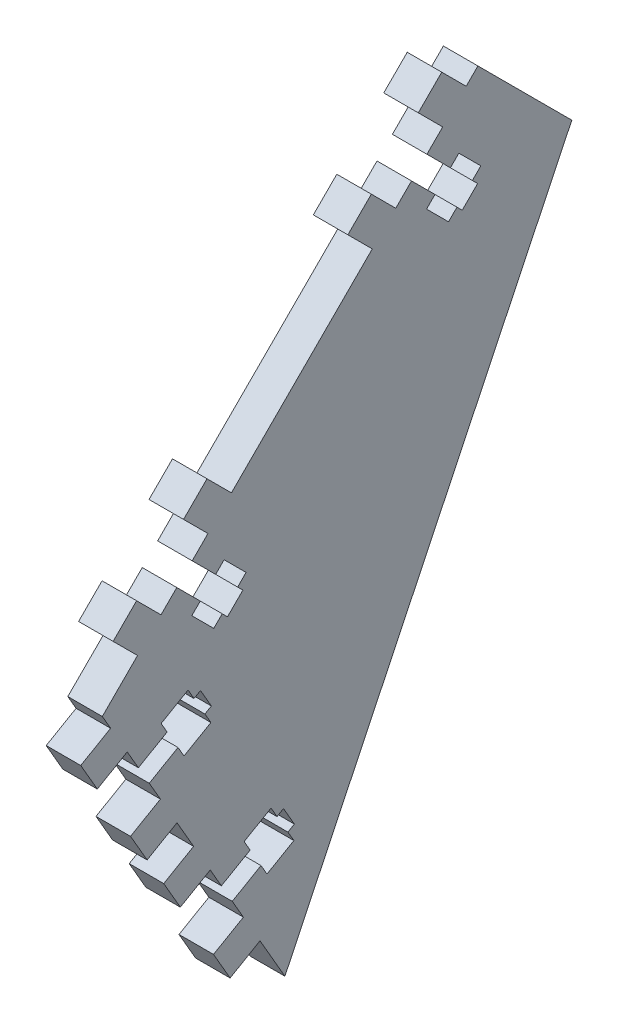
SolidWorks part; units mm, degrees
material "Acrylic (Blue)"
ref_plane "Front Plane" through (0, 0, 0) normal (0, 0, 1) x (1, 0, 0)
ref_plane "Top Plane" through (0, 0, 0) normal (0, 1, 0) x (1, 0, 0)
ref_plane "Right Plane" through (0, 0, 0) normal (1, 0, 0) x (0, 0, -1)
sketch "Sketch1" plane through (0, 0, 0) normal (1, 0, 0) x (0, 0, -1)
  line L0 (0, 0) -> (-34.925, 60.4919)
  line L2 (0, 0) -> (0, 247.8388) construction
  line L3 (0, 0) -> (101.6, 0) construction
  line L4 (0, 0) -> (54.8776, 114.3734)
  line L9 (54.8776, 114.3734) -> (36.917, 132.3339)
  line L10 (36.917, 132.3339) -> (-34.925, 60.4919)
  line B0 (24.219, 119.6358) -> (28.7091, 115.1457) construction
  line B1 (28.7091, 115.1457) -> (27.0926, 113.5293) construction
  line B2 (27.0926, 113.5293) -> (31.2954, 109.3265) construction
  line B3 (31.2954, 109.3265) -> (32.9119, 110.943) construction
  line B4 (32.9119, 110.943) -> (33.9176, 109.9372) construction
  line B5 (33.9176, 109.9372) -> (36.8632, 112.8827) construction
  line B6 (36.8632, 112.8827) -> (35.8574, 113.8885) construction
  line B7 (35.8574, 113.8885) -> (37.4738, 115.5049) construction
  line B8 (37.4738, 115.5049) -> (33.2711, 119.7077) construction
  line B9 (33.2711, 119.7077) -> (31.6546, 118.0912) construction
  line B10 (31.6546, 118.0912) -> (27.1645, 122.5814) construction
  line B11 (30.1819, 125.5987) -> (25.5121, 130.2685) construction
  line B12 (25.5121, 130.2685) -> (30.0023, 134.7586) construction
  line B13 (30.0023, 134.7586) -> (34.672, 130.0889) construction
  line B14 (24.219, 119.6358) -> (21.2016, 116.6185) construction
  line B15 (21.2016, 116.6185) -> (16.5319, 121.2882) construction
  line B16 (16.5319, 121.2882) -> (12.0417, 116.7981) construction
  line B17 (12.0417, 116.7981) -> (16.7115, 112.1283) construction
  line B18 (27.1645, 122.5814) -> (24.219, 119.6358) construction
  line B19 (-20.6823, 74.7346) -> (-16.1922, 70.2444) construction
  line B20 (-16.1922, 70.2444) -> (-17.8086, 68.628) construction
  line B21 (-17.8086, 68.628) -> (-13.6059, 64.4252) construction
  line B22 (-13.6059, 64.4252) -> (-11.9894, 66.0417) construction
  line B23 (-11.9894, 66.0417) -> (-10.9836, 65.0359) construction
  line B24 (-10.9836, 65.0359) -> (-8.0381, 67.9814) construction
  line B25 (-8.0381, 67.9814) -> (-9.0439, 68.9872) construction
  line B26 (-9.0439, 68.9872) -> (-7.4275, 70.6036) construction
  line B27 (-7.4275, 70.6036) -> (-11.6302, 74.8064) construction
  line B28 (-11.6302, 74.8064) -> (-13.2467, 73.19) construction
  line B29 (-13.2467, 73.19) -> (-17.7368, 77.6801) construction
  line B30 (-14.7194, 80.6975) -> (-19.3892, 85.3672) construction
  line B31 (-19.3892, 85.3672) -> (-14.899, 89.8573) construction
  line B32 (-14.899, 89.8573) -> (-10.2293, 85.1876) construction
  line B33 (-23.6997, 71.7172) -> (-28.3694, 76.3869) construction
  line B34 (-28.3694, 76.3869) -> (-32.8595, 71.8968) construction
  line B35 (-32.8595, 71.8968) -> (-28.1898, 67.2271) construction
  line B36 (-17.7368, 77.6801) -> (-20.6823, 74.7346) construction
  line B37 (-25.9461, 44.94) -> (-20.4468, 48.115) construction
  line B38 (-20.4468, 48.115) -> (-19.3038, 46.1352) construction
  line B39 (-19.3038, 46.1352) -> (-14.1565, 49.107) construction
  line B40 (-14.1565, 49.107) -> (-15.2995, 51.0868) construction
  line B41 (-15.2995, 51.0868) -> (-14.0677, 51.798) construction
  line B42 (-14.0677, 51.798) -> (-16.1505, 55.4055) construction
  line B43 (-16.1505, 55.4055) -> (-17.3823, 54.6943) construction
  line B44 (-17.3823, 54.6943) -> (-18.5253, 56.674) construction
  line B45 (-18.5253, 56.674) -> (-23.6726, 53.7022) construction
  line B46 (-23.6726, 53.7022) -> (-22.5296, 51.7225) construction
  line B47 (-22.5296, 51.7225) -> (-28.0289, 48.5475) construction
  line B48 (-28.0289, 48.5475) -> (-30.1625, 52.243) construction
  line B49 (-30.1625, 52.243) -> (-35.8817, 48.941) construction
  line B50 (-35.8817, 48.941) -> (-39.0567, 54.4402) construction
  line B51 (-39.0567, 54.4402) -> (-33.3375, 57.7422) construction
  line B52 (-25.9461, 44.94) -> (-23.8125, 41.2445) construction
  line B53 (-23.8125, 41.2445) -> (-29.5317, 37.9425) construction
  line B54 (-29.5317, 37.9425) -> (-26.3567, 32.4432) construction
  line B55 (-26.3567, 32.4432) -> (-20.6375, 35.7452) construction
  line B56 (-28.0289, 48.5475) -> (-25.9461, 44.94) construction
  line B57 (-10.0711, 17.4437) -> (-4.5718, 20.6187) construction
  line B58 (-4.5718, 20.6187) -> (-3.4288, 18.6389) construction
  line B59 (-3.4288, 18.6389) -> (1.7185, 21.6107) construction
  line B60 (1.7185, 21.6107) -> (0.5755, 23.5905) construction
  line B61 (0.5755, 23.5905) -> (1.8073, 24.3017) construction
  line B62 (1.8073, 24.3017) -> (-0.2755, 27.9092) construction
  line B63 (-0.2755, 27.9092) -> (-1.5073, 27.198) construction
  line B64 (-1.5073, 27.198) -> (-2.6503, 29.1777) construction
  line B65 (-2.6503, 29.1777) -> (-7.7976, 26.2059) construction
  line B66 (-7.7976, 26.2059) -> (-6.6546, 24.2262) construction
  line B67 (-6.6546, 24.2262) -> (-12.1539, 21.0512) construction
  line B68 (-14.2875, 24.7467) -> (-20.0067, 21.4447) construction
  line B69 (-20.0067, 21.4447) -> (-23.1817, 26.9439) construction
  line B70 (-23.1817, 26.9439) -> (-17.4625, 30.2459) construction
  line B71 (-7.9375, 13.7482) -> (-13.6567, 10.4462) construction
  line B72 (-13.6567, 10.4462) -> (-10.4817, 4.9469) construction
  line B73 (-10.4817, 4.9469) -> (-4.7625, 8.2489) construction
  line B74 (-12.1539, 21.0512) -> (-10.0711, 17.4437) construction
  dimension "D1" = 30
  dimension "D2" = 69.85
  dimension "D3" = 101.6
  dimension "D4" = 19.05
  dimension "D5" = 3.175
  dimension "D6" = 25.4
  dimension "D7" = 135
  dimension "D8" = 44.45
  dimension "D9" = 3.175
  dimension "D11" = 101.6
sketch_block_instance "NUT_HOLE-1"
sketch_block "NUT_HOLE" parameters "D1"=6.35, "D2"=4.1656, "D3"=25.4, "D4"=6.604, "D5"=8.7376, "D6"=5.9436, "D7"=6.35, "D8"=20.32
sketch_block_instance "NUT_HOLE-2"
sketch_block_instance "NUT_HOLE-3"
sketch_block_instance "NUT_HOLE-4"
extrude "Boss-Extrude1" add sketch "Sketch1" against normal blind 6.604
sketch "Sketch2" plane through (0, 0, 0) normal (1, 0, 0) x (0, 0, -1)
  line L0 (31.6546, 118.0912) -> (27.1645, 122.5814) construction
  line L1 (24.219, 119.6358) -> (28.7091, 115.1457) construction
  line L2 (28.7091, 115.1457) -> (27.0926, 113.5293) construction
  line L3 (33.2711, 119.7077) -> (31.6546, 118.0912) construction
  line L4 (37.4738, 115.5049) -> (33.2711, 119.7077) construction
  line L5 (35.8574, 113.8885) -> (37.4738, 115.5049) construction
  line L6 (36.8632, 112.8827) -> (35.8574, 113.8885) construction
  line L7 (33.9176, 109.9372) -> (36.8632, 112.8827) construction
  line L8 (32.9119, 110.943) -> (33.9176, 109.9372) construction
  line L9 (31.2954, 109.3265) -> (32.9119, 110.943) construction
  line L10 (27.0926, 113.5293) -> (31.2954, 109.3265) construction
  line L11 (-13.2467, 73.19) -> (-17.7368, 77.6801) construction
  line L12 (-20.6823, 74.7346) -> (-16.1922, 70.2444) construction
  line L13 (-16.1922, 70.2444) -> (-17.8086, 68.628) construction
  line L14 (-17.8086, 68.628) -> (-13.6059, 64.4252) construction
  line L15 (-13.6059, 64.4252) -> (-11.9894, 66.0417) construction
  line L16 (-11.9894, 66.0417) -> (-10.9836, 65.0359) construction
  line L17 (-10.9836, 65.0359) -> (-8.0381, 67.9814) construction
  line L18 (-9.0439, 68.9872) -> (-7.4275, 70.6036) construction
  line L19 (-8.0381, 67.9814) -> (-9.0439, 68.9872) construction
  line L20 (-7.4275, 70.6036) -> (-11.6302, 74.8064) construction
  line L21 (-11.6302, 74.8064) -> (-13.2467, 73.19) construction
  line L22 (-17.3823, 54.6943) -> (-18.5253, 56.674) construction
  line L23 (-16.1505, 55.4055) -> (-17.3823, 54.6943) construction
  line L24 (-14.0677, 51.798) -> (-16.1505, 55.4055) construction
  line L25 (-15.2995, 51.0868) -> (-14.0677, 51.798) construction
  line L26 (-14.1565, 49.107) -> (-15.2995, 51.0868) construction
  line L27 (-19.3038, 46.1352) -> (-14.1565, 49.107) construction
  line L28 (-20.4468, 48.115) -> (-19.3038, 46.1352) construction
  line L29 (-25.9461, 44.94) -> (-20.4468, 48.115) construction
  line L30 (-22.5296, 51.7225) -> (-28.0289, 48.5475) construction
  line L31 (-23.6726, 53.7022) -> (-22.5296, 51.7225) construction
  line L32 (-18.5253, 56.674) -> (-23.6726, 53.7022) construction
  line L33 (-2.6503, 29.1777) -> (-7.7976, 26.2059) construction
  line L34 (-7.7976, 26.2059) -> (-6.6546, 24.2262) construction
  line L35 (-6.6546, 24.2262) -> (-12.1539, 21.0512) construction
  line L36 (-10.0711, 17.4437) -> (-4.5718, 20.6187) construction
  line L37 (-4.5718, 20.6187) -> (-3.4288, 18.6389) construction
  line L38 (-3.4288, 18.6389) -> (1.7185, 21.6107) construction
  line L39 (1.7185, 21.6107) -> (0.5755, 23.5905) construction
  line L40 (0.5755, 23.5905) -> (1.8073, 24.3017) construction
  line L41 (1.8073, 24.3017) -> (-0.2755, 27.9092) construction
  line L42 (-0.2755, 27.9092) -> (-1.5073, 27.198) construction
  line L43 (-1.5073, 27.198) -> (-2.6503, 29.1777) construction
  line L44 (31.6546, 118.0912) -> (27.1645, 122.5814)
  line L45 (24.219, 119.6358) -> (28.7091, 115.1457)
  line L46 (28.7091, 115.1457) -> (27.0926, 113.5293)
  line L47 (33.2711, 119.7077) -> (31.6546, 118.0912)
  line L48 (37.4738, 115.5049) -> (33.2711, 119.7077)
  line L49 (35.8574, 113.8885) -> (37.4738, 115.5049)
  line L50 (36.8632, 112.8827) -> (35.8574, 113.8885)
  line L51 (33.9176, 109.9372) -> (36.8632, 112.8827)
  line L52 (32.9119, 110.943) -> (33.9176, 109.9372)
  line L53 (31.2954, 109.3265) -> (32.9119, 110.943)
  line L54 (27.0926, 113.5293) -> (31.2954, 109.3265)
  line L55 (-13.2467, 73.19) -> (-17.7368, 77.6801)
  line L56 (-20.6823, 74.7346) -> (-16.1922, 70.2444)
  line L57 (-16.1922, 70.2444) -> (-17.8086, 68.628)
  line L58 (-17.8086, 68.628) -> (-13.6059, 64.4252)
  line L59 (-13.6059, 64.4252) -> (-11.9894, 66.0417)
  line L60 (-11.9894, 66.0417) -> (-10.9836, 65.0359)
  line L61 (-10.9836, 65.0359) -> (-8.0381, 67.9814)
  line L62 (-9.0439, 68.9872) -> (-7.4275, 70.6036)
  line L63 (-8.0381, 67.9814) -> (-9.0439, 68.9872)
  line L64 (-7.4275, 70.6036) -> (-11.6302, 74.8064)
  line L65 (-11.6302, 74.8064) -> (-13.2467, 73.19)
  line L66 (-17.3823, 54.6943) -> (-18.5253, 56.674)
  line L67 (-16.1505, 55.4055) -> (-17.3823, 54.6943)
  line L68 (-14.0677, 51.798) -> (-16.1505, 55.4055)
  line L69 (-15.2995, 51.0868) -> (-14.0677, 51.798)
  line L70 (-14.1565, 49.107) -> (-15.2995, 51.0868)
  line L71 (-19.3038, 46.1352) -> (-14.1565, 49.107)
  line L72 (-20.4468, 48.115) -> (-19.3038, 46.1352)
  line L73 (-25.9461, 44.94) -> (-20.4468, 48.115)
  line L74 (-22.5296, 51.7225) -> (-28.0289, 48.5475)
  line L75 (-23.6726, 53.7022) -> (-22.5296, 51.7225)
  line L76 (-18.5253, 56.674) -> (-23.6726, 53.7022)
  line L77 (-2.6503, 29.1777) -> (-7.7976, 26.2059)
  line L78 (-7.7976, 26.2059) -> (-6.6546, 24.2262)
  line L79 (-6.6546, 24.2262) -> (-12.1539, 21.0512)
  line L80 (-10.0711, 17.4437) -> (-4.5718, 20.6187)
  line L81 (-4.5718, 20.6187) -> (-3.4288, 18.6389)
  line L82 (-3.4288, 18.6389) -> (1.7185, 21.6107)
  line L83 (1.7185, 21.6107) -> (0.5755, 23.5905)
  line L84 (0.5755, 23.5905) -> (1.8073, 24.3017)
  line L85 (1.8073, 24.3017) -> (-0.2755, 27.9092)
  line L86 (-0.2755, 27.9092) -> (-1.5073, 27.198)
  line L87 (-1.5073, 27.198) -> (-2.6503, 29.1777)
  line L88 (27.1645, 122.5814) -> (24.219, 119.6358)
  line L89 (-20.6823, 74.7346) -> (-17.7368, 77.6801)
  line L90 (-28.0289, 48.5475) -> (-25.9461, 44.94)
  line L91 (-12.1539, 21.0512) -> (-10.0711, 17.4437)
  point P0 (-18.5253, 56.674)
extrude "Cut-Extrude1" cut sketch "Sketch2" against normal through all
sketch "Sketch3" plane through (0, 0, 0) normal (1, 0, 0) x (0, 0, -1)
  line L0 (30.0023, 134.7586) -> (34.672, 130.0889) construction
  line L1 (25.5121, 130.2685) -> (30.0023, 134.7586) construction
  line L2 (30.1819, 125.5987) -> (25.5121, 130.2685) construction
  line L3 (21.2016, 116.6185) -> (16.5319, 121.2882) construction
  line L4 (16.5319, 121.2882) -> (12.0417, 116.7981) construction
  line L5 (12.0417, 116.7981) -> (16.7115, 112.1283) construction
  line L6 (-14.7194, 80.6975) -> (-19.3892, 85.3672) construction
  line L7 (-19.3892, 85.3672) -> (-14.899, 89.8573) construction
  line L8 (-14.899, 89.8573) -> (-10.2293, 85.1876) construction
  line L9 (-28.3694, 76.3869) -> (-32.8595, 71.8968) construction
  line L10 (-23.6997, 71.7172) -> (-28.3694, 76.3869) construction
  line L11 (-32.8595, 71.8968) -> (-28.1898, 67.2271) construction
  line L12 (-39.0567, 54.4402) -> (-33.3375, 57.7422) construction
  line L13 (-35.8817, 48.941) -> (-39.0567, 54.4402) construction
  line L14 (-23.8125, 41.2445) -> (-29.5317, 37.9425) construction
  line L15 (-29.5317, 37.9425) -> (-26.3567, 32.4432) construction
  line L16 (-26.3567, 32.4432) -> (-20.6375, 35.7452) construction
  line L17 (-23.1817, 26.9439) -> (-17.4625, 30.2459) construction
  line L18 (-20.0067, 21.4447) -> (-23.1817, 26.9439) construction
  line L19 (-14.2875, 24.7467) -> (-20.0067, 21.4447) construction
  line L20 (-13.6567, 10.4462) -> (-10.4817, 4.9469) construction
  line L21 (-10.4817, 4.9469) -> (-4.7625, 8.2489) construction
  line L22 (-7.9375, 13.7482) -> (-13.6567, 10.4462) construction
  line L23 (30.0023, 134.7586) -> (34.672, 130.0889)
  line L24 (25.5121, 130.2685) -> (30.0023, 134.7586)
  line L25 (30.1819, 125.5987) -> (25.5121, 130.2685)
  line L26 (21.2016, 116.6185) -> (16.5319, 121.2882)
  line L27 (16.5319, 121.2882) -> (12.0417, 116.7981)
  line L28 (12.0417, 116.7981) -> (16.7115, 112.1283)
  line L29 (-14.7194, 80.6975) -> (-19.3892, 85.3672)
  line L30 (-19.3892, 85.3672) -> (-14.899, 89.8573)
  line L31 (-14.899, 89.8573) -> (-10.2293, 85.1876)
  line L32 (-28.3694, 76.3869) -> (-32.8595, 71.8968)
  line L33 (-23.6997, 71.7172) -> (-28.3694, 76.3869)
  line L34 (-32.8595, 71.8968) -> (-28.1898, 67.2271)
  line L35 (-39.0567, 54.4402) -> (-33.3375, 57.7422)
  line L36 (-35.8817, 48.941) -> (-39.0567, 54.4402)
  line L37 (-23.8125, 41.2445) -> (-29.5317, 37.9425)
  line L38 (-29.5317, 37.9425) -> (-26.3567, 32.4432)
  line L39 (-26.3567, 32.4432) -> (-20.6375, 35.7452)
  line L40 (-23.1817, 26.9439) -> (-17.4625, 30.2459)
  line L41 (-20.0067, 21.4447) -> (-23.1817, 26.9439)
  line L42 (-14.2875, 24.7467) -> (-20.0067, 21.4447)
  line L43 (-13.6567, 10.4462) -> (-10.4817, 4.9469)
  line L44 (-10.4817, 4.9469) -> (-4.7625, 8.2489)
  line L45 (-7.9375, 13.7482) -> (-13.6567, 10.4462)
  line L46 (34.672, 130.0889) -> (30.1819, 125.5987)
  line L47 (21.2016, 116.6185) -> (16.7115, 112.1283)
  line L48 (-10.2293, 85.1876) -> (-14.7194, 80.6975)
  line L49 (-23.6997, 71.7172) -> (-28.1898, 67.2271)
  line L50 (-33.3375, 57.7422) -> (-30.1625, 52.243)
  line L51 (-23.8125, 41.2445) -> (-20.6375, 35.7452)
  line L52 (-17.4625, 30.2459) -> (-14.2875, 24.7467)
  line L54 (-7.9375, 13.7482) -> (-4.7625, 8.2489)
  line L55 (-30.1625, 52.243) -> (-35.8817, 48.941) construction
  line L56 (-30.1625, 52.243) -> (-35.8817, 48.941)
extrude "Boss-Extrude2" add sketch "Sketch3" against normal up to surface (6.604 mm away) up to face at (-6.604, 65.8583, 0.0309)
other "Move Face1" [suppressed] parameters "D1"=0.0508
